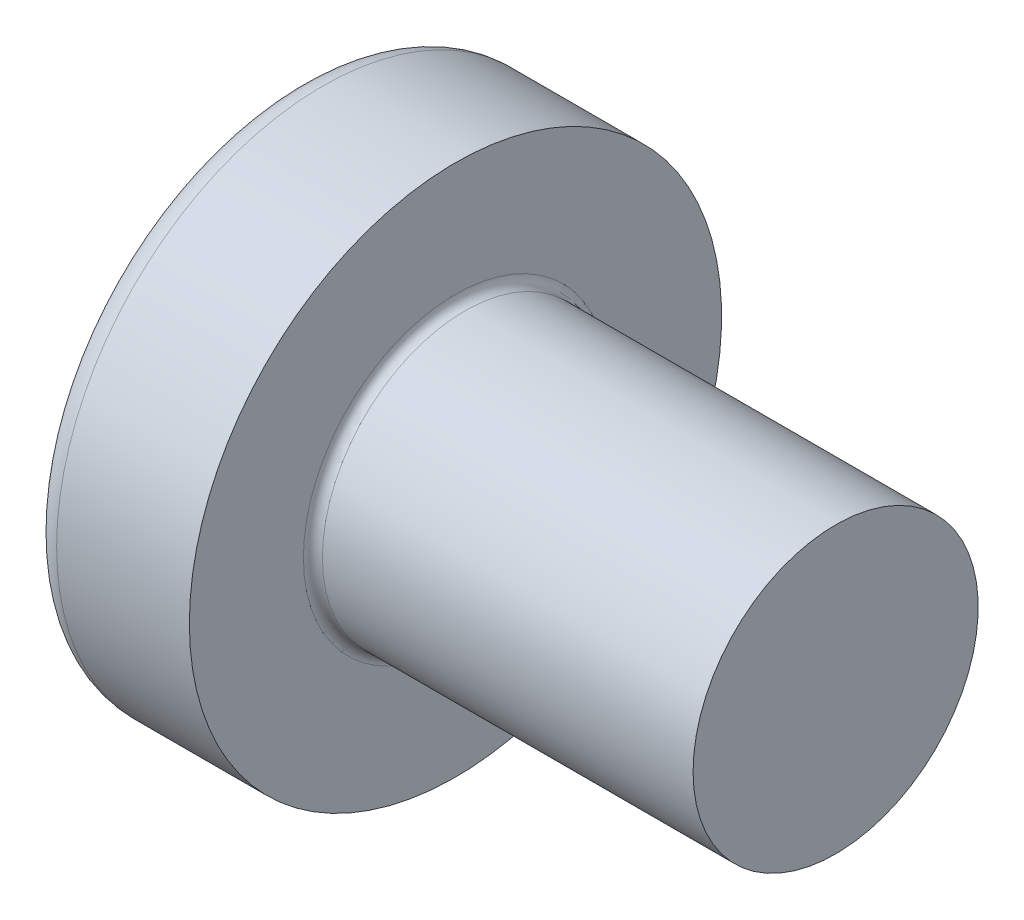
SolidWorks part; units mm, degrees
ref_plane "Plane1" through (0, 0, 0) normal (0, 0, 1) x (1, 0, 0)
ref_plane "Plane2" through (0, 0, 0) normal (0, 1, 0) x (1, 0, 0)
ref_plane "Plane3" through (0, 0, 0) normal (1, 0, 0) x (0, 0, -1)
sketch "BodySke" plane through (0, 0, 0) normal (0, 0, 1) x (1, 0, 0)
  line L0 (2.4, 1.5) -> (2.4, 2.8)
  line L1 (2.65, 6.35) -> (2.65, -3.175) construction
  line L2 (-25.4, 0) -> (127, 0) construction
  line L3 (6.4, 0) -> (0, 0)
  line L4 (2.4, 1.5) -> (6.4, 1.5)
  line L5 (6.4, 1.5) -> (6.4, 0)
  line L6 (1.0035, 2.8) -> (2.4, 2.8)
  line L8 (2.4, 6.35) -> (2.4, -3.175) construction
  arc A0 (0.7754, 2.6744) -> (0, 0) centre (5, 0) ccw
  arc A2 (0.7754, 2.6744) -> (1.0035, 2.8) centre (1.0035, 2.53) cw
  dimension "Head_crown_rad" = 5
  dimension "Head_fillet_rad" = 0.27
  dimension "Length" = 4
  dimension "Head_ht" = 2.4
  dimension "Head_dia" = 5.6
  dimension "Advance" = 0.5
  dimension "Thread_nom" = 4
  dimension "Diameter" = 3
revolve "Base-Revolve" add sketch "BodySke"
cosmetic thread "ThreadCosmetic" [suppressed]
fillet "Fillet1" radius 0.1 1 edges at (2.4, 0, 1.5)
sketch "Sketch3" plane through (0, 0, 0) normal (1, 0, 0) x (0, 0, -1)
  line L0 (0.37, -1.4) -> (-0.37, -1.4)
  line L1 (0.37, -1.4) -> (0.37, 1.4)
  line L2 (-0.37, 1.4) -> (0.37, 1.4)
  line L3 (-0.37, 1.4) -> (-0.37, -1.4)
  dimension "Cross_dia" = 2.8
  dimension "D1" = 1.4
  dimension "Cross_width" = 0.74
  dimension "D2" = 0.37
ref_plane "Plane4" through (1.75, 0, 0) normal (1, 0, 0) x (0, 0, -1)
sketch "Sketch4" plane through (1.75, 0, 0) normal (1, 0, 0) x (0, 0, -1)
  line L0 (0.37, -0.5275) -> (-0.37, -0.5275)
  line L1 (0.37, -0.5275) -> (0.37, 0.5275)
  line L2 (-0.37, 0.5275) -> (0.37, 0.5275)
  line L3 (-0.37, 0.5275) -> (-0.37, -0.5275)
  dimension "D1" = 0.74
  dimension "D2" = 1.055
  dimension "D3" = 0.37
  dimension "D4" = 0.5275
loft "Recess" cut profiles "Sketch3", "Sketch4"
pattern_circular "RecPat" count 2 every 90 about axis through (0, 0, 0) along (1, 0, 0) of "Recess"
sketch "RecCorSke" plane through (0, 0, 0) normal (0, 0, 1) x (1, 0, 0)
  line L0 (-3.175, 0) -> (15.875, 0) construction
  line L1 (-25.4, 0) -> (127, 0) construction
  line L2 (0, 0) -> (0, 0.6784)
  line L3 (0, 0.6784) -> (1.75, 0.556)
  line L4 (1.75, 0.556) -> (1.9307, 0)
  line L5 (1.9307, 0) -> (0, 0)
  dimension "Diameter" = 1.112
  dimension "Depth" = 1.75
  dimension "Draft_angle" = 4
  dimension "Bottom_angle" = 18
revolve "RecessCore" cut sketch "RecCorSke" angle 360 about L0
sketch "ThdSchSke" plane through (0, 0, 0) normal (0, 0, 1) x (1, 0, 0)
  line L0 (3.4, -1.2195) -> (3.2036, -1.5)
  line L1 (3.4, -1.2195) -> (3.5964, -1.5)
  line L2 (3.5964, -1.5) -> (3.5964, -1.875)
  line L3 (-3.175, 0) -> (5.1513, 0) construction
  line L5 (3.5964, -1.875) -> (3.2036, -1.875)
  line L6 (3.2036, -1.875) -> (3.2036, -1.5)
  dimension "Diameter" = 3
  dimension "SideAngle" = 55
  dimension "VeeAngle" = 70
  dimension "Thread_minor" = 2.439
  dimension "Overcut" = 3.75
  dimension "Start" = 3.4
revolve "ThreadSchematic" [suppressed] cut sketch "ThdSchSke" angle 360 about L3
pattern_linear "ThdSchPat" [suppressed]
equation "\"D1@Sketch3\" = \"Cross_dia@Sketch3\" / 2"
equation "\"D2@Sketch3\" = \"Cross_width@Sketch3\" / 2"
equation "\"Depth@RecCorSke\" = \"Cross_depth@Plane4\""
equation "\"D1@Sketch4\" = \"Cross_width@Sketch3\""
equation "\"D2@Sketch4\" = \"Cross_dia@Sketch3\" - 2.0 * \"Cross_depth@Plane4\" * tan(26.5  * 0.017453292)"
equation "\"D3@Sketch4\" = \"D1@Sketch4\" / 2"
equation "\"D4@Sketch4\" = \"D2@Sketch4\" / 2"
equation "\"Thread_length@ThreadCosmetic\" = ((sgn( (\"Length@BodySke\" - \"Advance@BodySke\" * 2.0 ) - \"Thread_nom@BodySke\" )-1)*( (\"Length@BodySke\" - \"Advance@BodySke\" * 2.0 ) - \"Thread_nom@BodySke\" ))/-2+ \"Thread_nom@BodySke\""
equation "\"Thread_minor@ThdSchSke\" = \"Thread_minor@ThreadCosmetic\""
equation "\"Diameter@ThdSchSke\" = \"Diameter@BodySke\""
equation "\"Overcut@ThdSchSke\" = \"Diameter@BodySke\" * 1.25"
equation "\"Start@ThdSchSke\" = \"Head_ht@BodySke\" + \"Length@BodySke\" - \"Thread_length@ThreadCosmetic\"  '---Non-countersunk---"
equation "\"Num_threads@ThdSchPat\" = int( \"Thread_length@ThreadCosmetic\" / \"Advance@BodySke\" + 0.999 )  + 1"
equation "\"Advance@ThdSchPat\" = \"Thread_length@ThreadCosmetic\" /  (\"Num_threads@ThdSchPat\" - 1) 'relax it"
